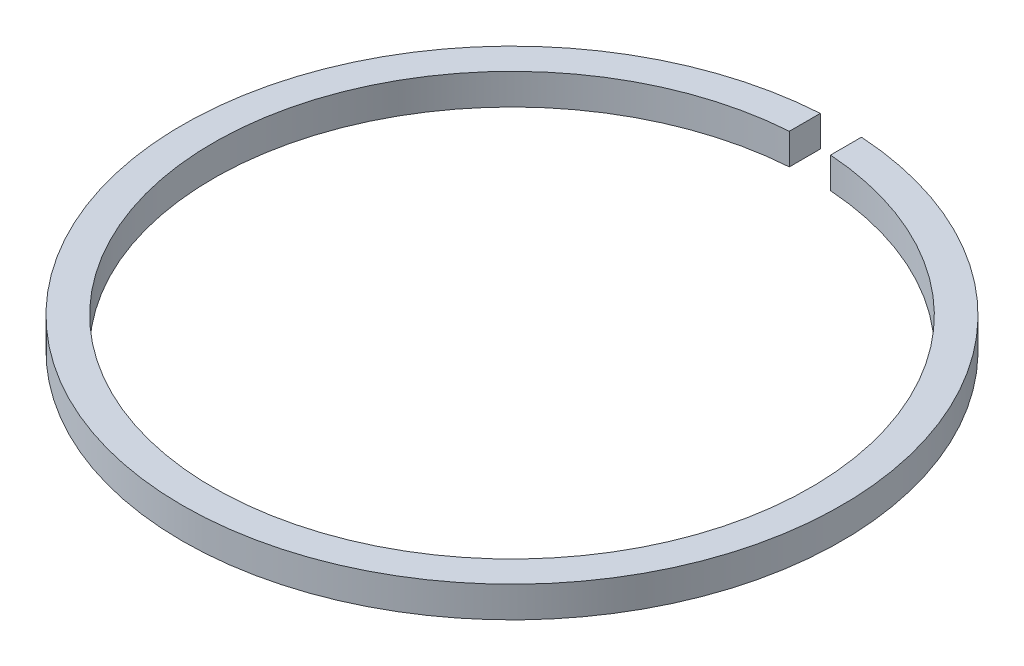
SolidWorks part; units mm, degrees
ref_plane "Front Plane" through (0, 0, 0) normal (0, 0, 1) x (1, 0, 0)
ref_plane "Top Plane" through (0, 0, 0) normal (0, 1, 0) x (1, 0, 0)
ref_plane "Right Plane" through (0, 0, 0) normal (1, 0, 0) x (0, 0, -1)
sketch "Sketch1" plane through (0, 0, 0) normal (0, 1, 0) x (1, 0, 0)
  line L0 (0, 0) -> (0, -21.1124) construction
  line L1 (-1, 14.4655) -> (-1, 15.9687)
  line L2 (1, 14.4655) -> (1, 15.9687)
  arc A0 (-1, 14.4655) -> (1, 14.4655) centre (0, 0) ccw
  arc A1 (-1, 15.9687) -> (1, 15.9687) centre (0, 0) ccw
  dimension "D1" = 32
  dimension "D2" = 29
  dimension "D3" = 2
  dimension "D4" = 1
extrude "Boss-Extrude1" add sketch "Sketch1" along normal blind 1.5
